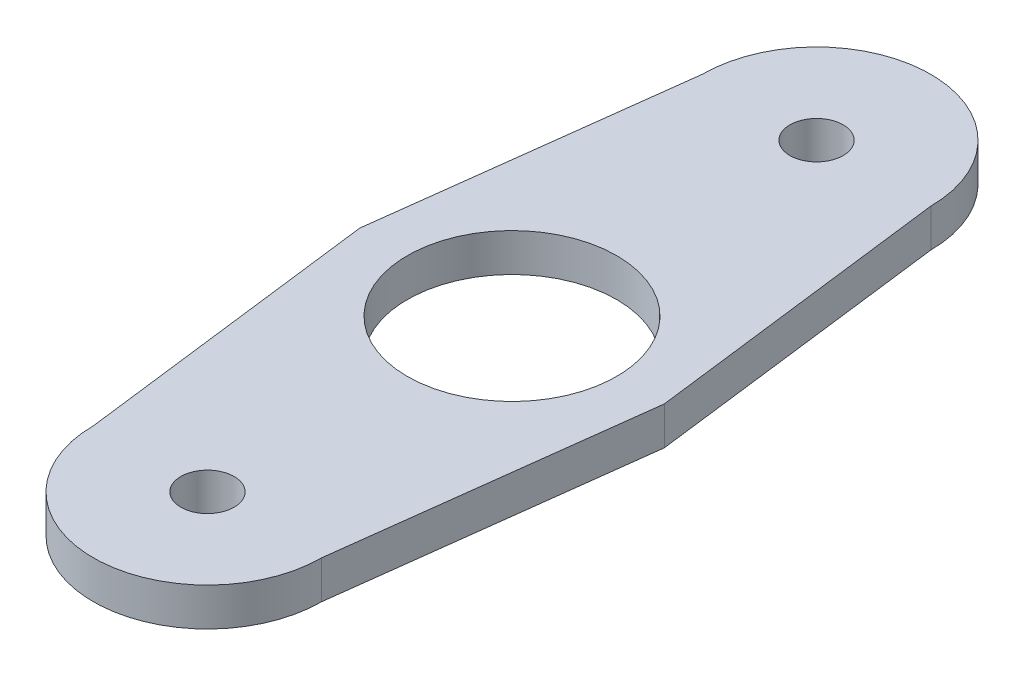
SolidWorks part; units mm, degrees
material "ABS"
ref_plane "Front Plane" through (0, 0, 0) normal (0, 0, 1) x (1, 0, 0)
ref_plane "Top Plane" through (0, 0, 0) normal (0, 1, 0) x (1, 0, 0)
ref_plane "Right Plane" through (0, 0, 0) normal (1, 0, 0) x (0, 0, -1)
sketch "Sketch1" plane through (0, 0, 0) normal (0, 1, 0) x (1, 0, 0)
  line L0 (0, -50.8) -> (0, 50.8)
  line L1 (19.05, 50.8) -> (25.4, 0)
  line L2 (-25.4, 0) -> (-19.05, 50.8)
  line L3 (-19.05, -50.8) -> (-25.4, 0)
  line L4 (19.05, -50.8) -> (25.4, 0)
  circle A0 centre (0, 0) radius 17.4625
  circle A1 centre (0, 0) radius 25.4 construction
  circle A2 centre (0, 50.8) radius 19.05
  circle A3 centre (0, -50.8) radius 19.05
  circle A4 centre (0, 50.8) radius 4.445
  circle A5 centre (0, -50.8) radius 4.445
  point P11 (0, 0)
  point P18 (0, 0)
  dimension "D1" = 34.925
  dimension "D2" = 50.8
  dimension "D3" = 38.1
  dimension "D4" = 38.1
  dimension "D5" = 101.6
  dimension "D6" = 8.89
  dimension "D7" = 8.89
extrude "Boss-Extrude1" add sketch "Sketch1" along normal blind 6.35
